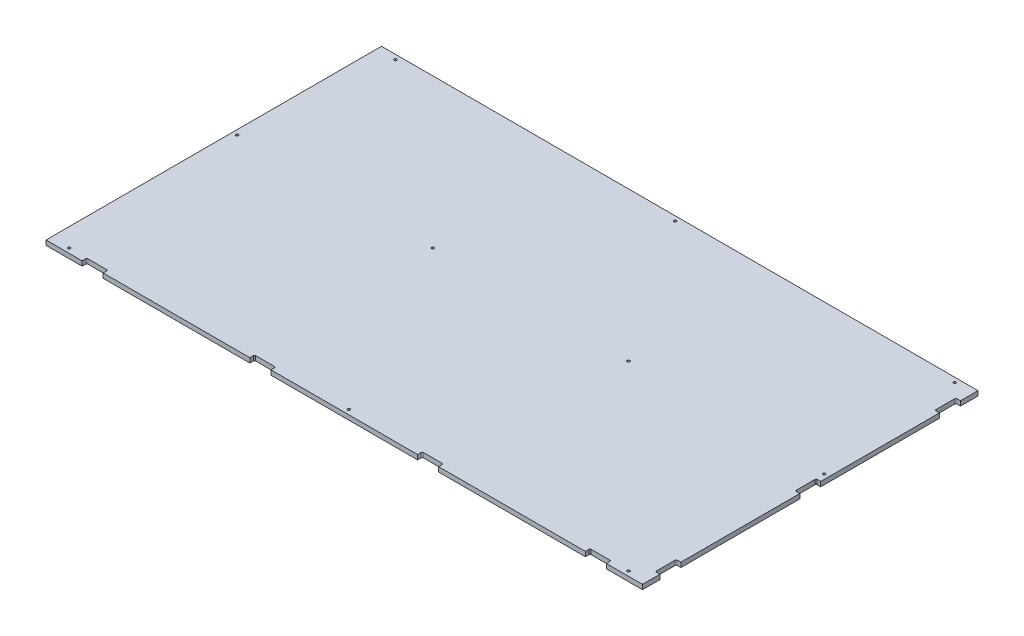
SolidWorks part; units mm, degrees
material "PE High Density"
ref_plane "Front Plane" through (0, 0, 0) normal (0, 0, 1) x (1, 0, 0)
ref_plane "Top Plane" through (0, 0, 0) normal (0, 1, 0) x (1, 0, 0)
ref_plane "Right Plane" through (0, 0, 0) normal (1, 0, 0) x (0, 0, -1)
sketch "Sketch1" plane through (0, 0, 0) normal (0, 1, 0) x (1, 0, 0)
  line L1 (0, 0) -> (1625.6, 0)
  line L2 (0, 0) -> (0, 914.4)
  line L3 (0, 914.4) -> (1625.6, 914.4)
  line L4 (1625.6, 0) -> (1625.6, 914.4)
  dimension "D1" = 1625.6
  dimension "D2" = 914.4
extrude "Boss-Extrude1" add sketch "Sketch1" along normal blind 12.7
sketch "Sketch2" plane through (0, 0, 0) normal (0, 1, 0) x (1, 0, 0)
  line L1 (1625.6, 914.4) -> (0, 914.4) construction
  line L2 (0, 914.4) -> (0, 0) construction
  line L3 (0, 0) -> (1625.6, 0) construction
  line L4 (1625.6, 0) -> (1625.6, 914.4) construction
  point P0 (12.7, 508)
  point P2 (546.1, 508)
  point P3 (1079.5, 508)
  point P4 (1612.9, 508)
  point P6 (50.8, 12.7)
  point P7 (812.8, 12.7)
  point P8 (1574.8, 12.7)
  point P9 (1574.8, 901.7)
  point P10 (812.8, 901.7)
  point P11 (50.8, 901.7)
  point P20 (812.8, 914.4)
  dimension "D1" = 12.7
  dimension "D2" = 12.7
  dimension "D3" = 12.7
  dimension "D4" = 12.7
  dimension "D5" = 266.7
  dimension "D6" = 533.4
  dimension "D7" = 762
  dimension "D8" = 762
  dimension "D10" = 406.4
hole_wizard "CSK for 1/4 Flat Head Machine Screw (100)1" positions "Sketch7" profile "Sketch8" countersink size "1/4" standard "ANSI Inch" end condition through all
sketch "Sketch7" plane through (0, 0, 0) normal (0, -1, 0) x (-1, 0, 0)
  point P0 (-50.8, 12.7)
  point P3 (-12.7, 508)
  point P6 (-50.8, 901.7)
  point P9 (-546.1, 508)
  point P12 (-1079.5, 508)
  point P15 (-812.8, 12.7)
  point P18 (-1574.8, 12.7)
  point P21 (-1574.8, 901.7)
  point P25 (-1612.9, 508)
  point P28 (-812.8, 901.7)
sketch "Sketch8" plane through (50.8, 0, -12.7) normal (1, 0, 0) x (0, 0, -1)
  line L0 (0, 0) -> (0, 12.7)
  line L1 (0, 12.7) -> (3.5712, 12.7)
  line L2 (3.5712, 12.7) -> (3.5712, 2.7579)
  line L3 (3.5712, 2.7579) -> (6.858, 0)
  line L5 (6.858, 0) -> (0, 0)
  line L6 (-3.5712, 2.7579) -> (-6.858, 0) construction
  line L11 (0, -6.35) -> (0, 107.95) construction
  dimension "Thru Hole Dia." = 7.1425
  dimension "Thru Hole Depth" = 12.7
  dimension "Near C'Sink Dia." = 13.716
  dimension "Near C'Sink Angle" = 100
sketch "Sketch5" plane through (0, 12.7, 0) normal (0, 1, 0) x (1, 0, 0)
  line L1 (98.425, 0) -> (155.575, 0)
  line L2 (98.425, 0) -> (98.425, 12.7)
  line L3 (98.425, 12.7) -> (155.575, 12.7)
  line L4 (155.575, 0) -> (155.575, 12.7)
  line L6 (0, 0) -> (1625.6, 0) construction
  line L7 (0, 914.4) -> (0, 0) construction
  dimension "D1" = 98.425
  dimension "D2" = 57.15
  dimension "D3" = 12.7
extrude "Cut-Extrude1" cut sketch "Sketch5" against normal through all
pattern_linear "LPattern1" count 4 spacing 457.2 along (1, 0, 0) of "Cut-Extrude1"
sketch "Sketch6" plane through (0, 12.7, 0) normal (0, 1, 0) x (1, 0, 0)
  line L0 (1625.6, 0) -> (1625.6, 914.4) construction
  line L1 (1625.6, 47.625) -> (1612.9, 47.625)
  line L2 (1625.6, 47.625) -> (1625.6, 104.775)
  line L3 (1625.6, 104.775) -> (1612.9, 104.775)
  line L4 (1612.9, 47.625) -> (1612.9, 104.775)
  line L5 (1527.175, 0) -> (1625.6, 0) construction
  dimension "D1" = 12.7
  dimension "D2" = 57.15
  dimension "D3" = 47.625
extrude "Cut-Extrude2" cut sketch "Sketch6" against normal through all
pattern_linear "LPattern2" count 3 spacing 381 along (0, 0, -1) of "Cut-Extrude2"
fillet "Fillet1" radius 3.175 14 edges at (1012.825, 6.35, -12.7) (555.625, 6.35, -12.7) (98.425, 6.35, -12.7) (155.575, 6.35, -12.7) (612.775, 6.35, -12.7) (1069.975, 6.35, -12.7) (1470.025, 6.35, -12.7) (1527.175, 6.35, -12.7) (1612.9, 6.35, -47.625) (1612.9, 6.35, -104.775) (1612.9, 6.35, -485.775) (1612.9, 6.35, -428.625) (1612.9, 6.35, -809.625) (1612.9, 6.35, -866.775)
